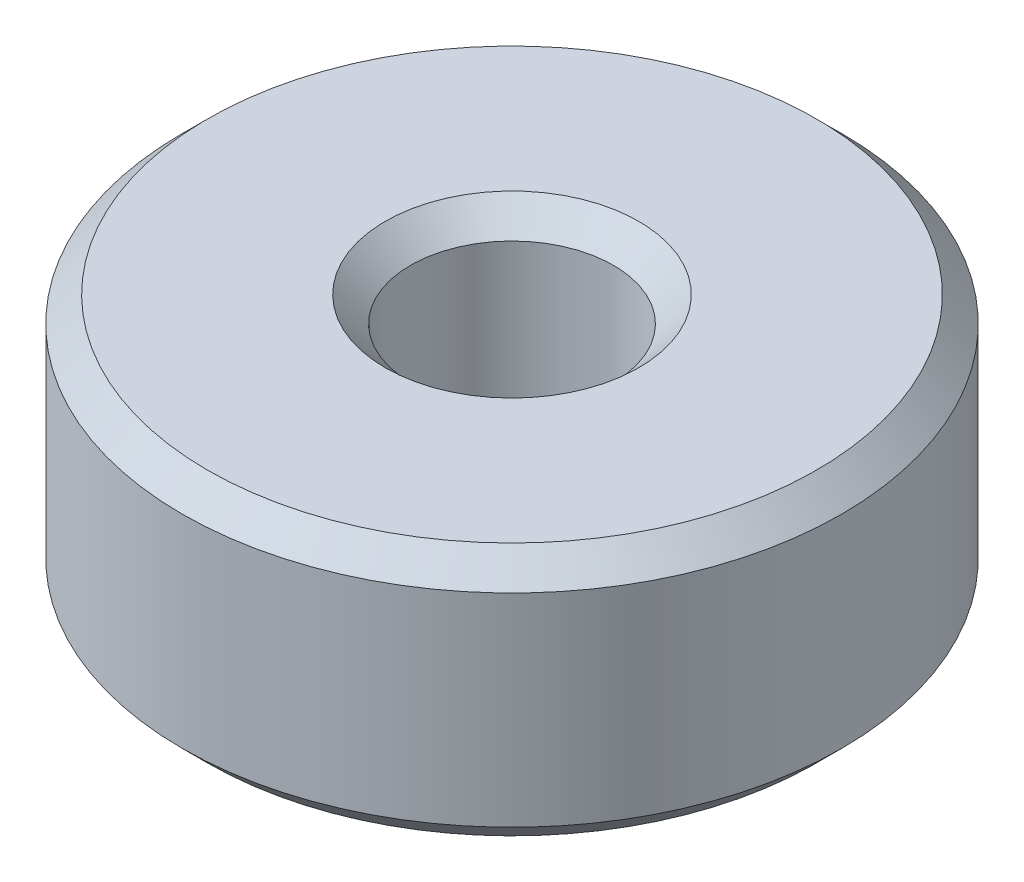
SolidWorks part; units mm, degrees
ref_plane "前视基准面" through (0, 0, 0) normal (0, 0, 1) x (1, 0, 0)
ref_plane "上视基准面" through (0, 0, 0) normal (0, 1, 0) x (1, 0, 0)
ref_plane "右视基准面" through (0, 0, 0) normal (1, 0, 0) x (0, 0, -1)
sketch "草图1" plane through (0, 0, 0) normal (0, 1, 0) x (1, 0, 0)
  circle A0 centre (0, 0) radius 6.5
  circle A1 centre (0, 0) radius 2
  dimension "D1" = 4
  dimension "D2" = 13
extrude "凸台-拉伸1" add sketch "草图1" along normal blind 5
chamfer "倒角1" distance 0.5 angle 45 4 edges at (0, 0, 2) (0, 5, 2) (0, 0, 6.5) (0, 5, 6.5)
